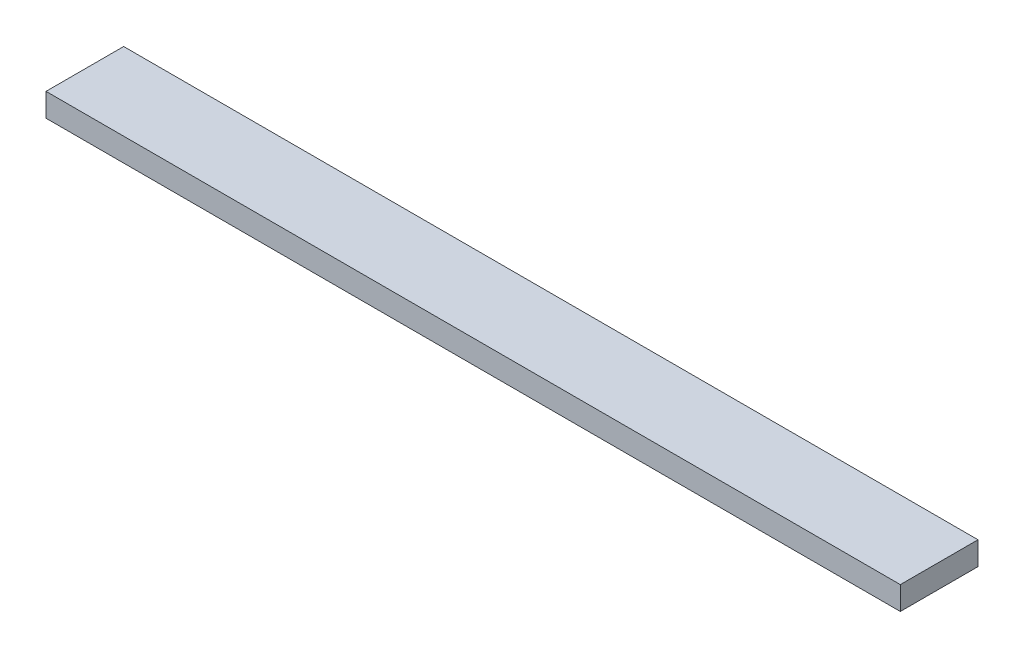
SolidWorks part; units mm, degrees
material "Beech"
ref_plane "Plane1" through (0, 0, 0) normal (0, 0, 1) x (1, 0, 0)
ref_plane "Plane2" through (0, 0, 0) normal (0, 1, 0) x (1, 0, 0)
ref_plane "Plane3" through (0, 0, 0) normal (1, 0, 0) x (0, 0, -1)
sketch "Sketch1" plane through (0, 0, 0) normal (0, 1, 0) x (1, 0, 0)
  line L1 (0, 0) -> (550, 0)
  line L2 (0, 0) -> (0, 50)
  line L3 (0, 50) -> (550, 50)
  line L4 (550, 0) -> (550, 50)
  dimension "D1" = 50
  dimension "D2" = 550
extrude "Boss-Extrude1" add sketch "Sketch1" along normal blind 15
